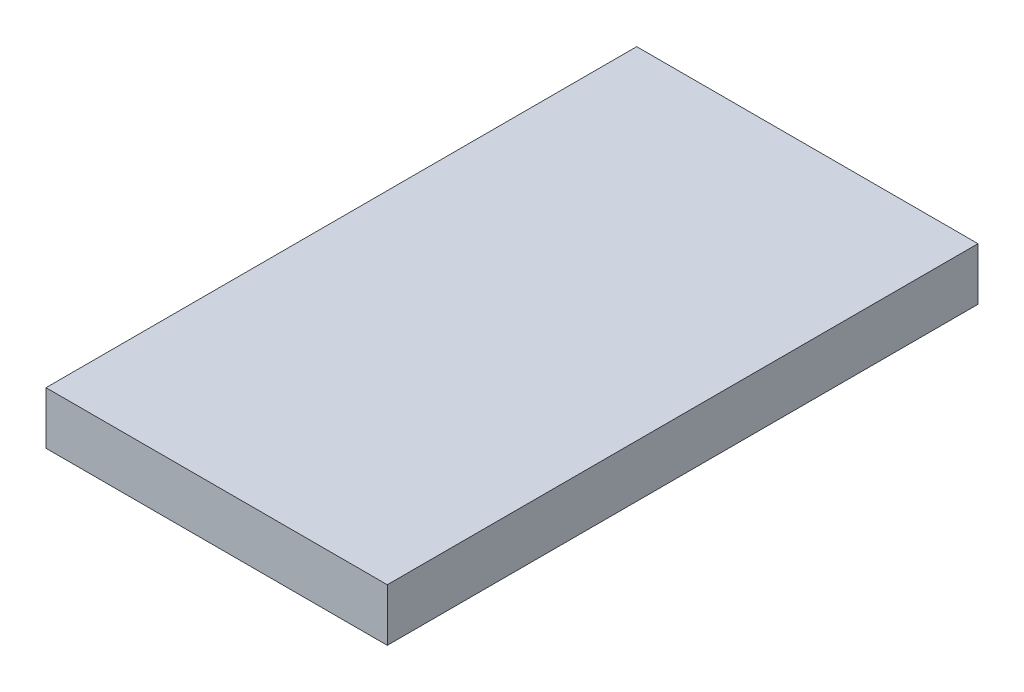
SolidWorks part; units mm, degrees
material "Silicon"
ref_plane "Front Plane" through (0, 0, 0) normal (0, 0, 1) x (1, 0, 0)
ref_plane "Top Plane" through (0, 0, 0) normal (0, 1, 0) x (1, 0, 0)
ref_plane "Right Plane" through (0, 0, 0) normal (1, 0, 0) x (0, 0, -1)
sketch "BaseS" plane through (0, 0, 0) normal (0, 1, 0) x (1, 0, 0)
  line L1 (-5.2, 9) -> (5.2, 9)
  line L2 (-5.2, 9) -> (-5.2, -9)
  line L3 (-5.2, -9) -> (5.2, -9)
  line L4 (5.2, 9) -> (5.2, -9)
  line L5 (-5.2, 9) -> (5.2, -9) construction
  line L6 (-5.2, -9) -> (5.2, 9) construction
  point P0 (0, 0)
  dimension "Width" = 10.4
  dimension "Length" = 18
extrude "Base" add sketch "BaseS" along normal blind 1.6
